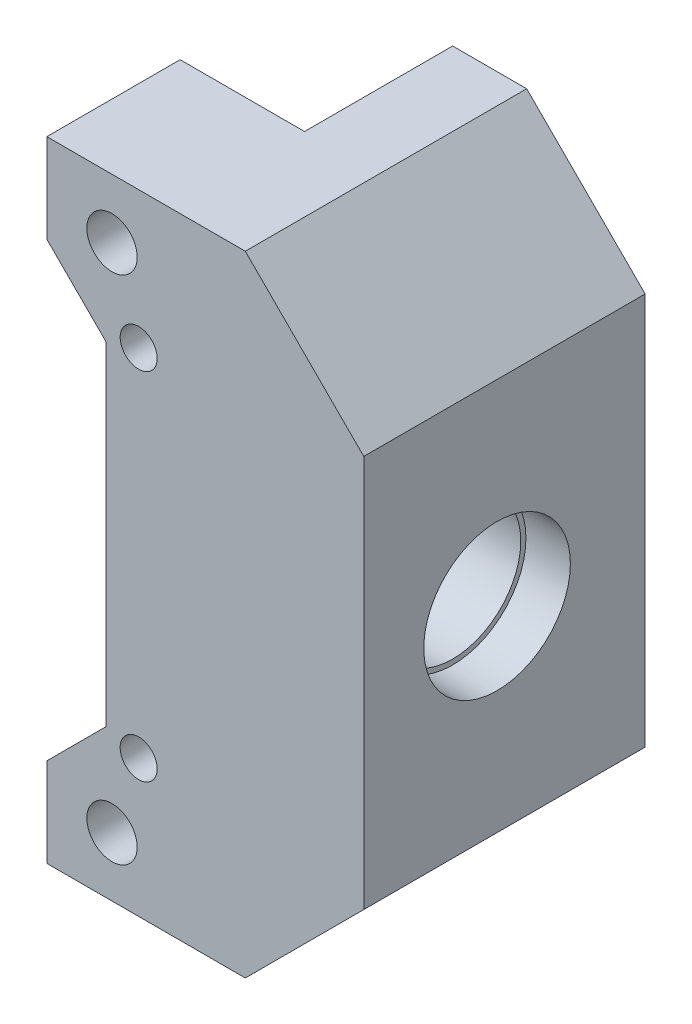
SolidWorks part; units mm, degrees
ref_plane "Plan de face" through (0, 0, 0) normal (0, 0, 1) x (1, 0, 0)
ref_plane "Plan de dessus" through (0, 0, 0) normal (0, 1, 0) x (1, 0, 0)
ref_plane "Plan de droite" through (0, 0, 0) normal (1, 0, 0) x (0, 0, -1)
sketch "Esquisse1" plane through (0, 0, 0) normal (0, 0, 1) x (1, 0, 0)
  line L0 (38.6155, 27.325) -> (38.6155, 15.175)
  line L1 (34.2155, 15.175) -> (34.2155, 27.325)
  line L6 (34.2155, 15.175) -> (34.2155, 10)
  line L7 (34.2155, 10) -> (30.2155, 6)
  line L8 (30.2155, 6) -> (30.2155, 0)
  line L9 (30.2155, 0) -> (38.6155, 0)
  line L10 (38.6155, 0) -> (38.6155, 15.175)
  line L11 (38.6155, 15.175) -> (34.2155, 15.175)
  line L12 (34.2155, 15.175) -> (34.2155, 10)
  line L13 (34.2155, 10) -> (30.2155, 6)
  line L14 (30.2155, 6) -> (30.2155, 0)
  line L15 (30.2155, 0) -> (38.6155, 0)
  line L16 (38.6155, 0) -> (38.6155, 15.175)
  line L18 (30.2155, 42.5) -> (30.2155, 36.5)
  line L19 (30.2155, 36.5) -> (34.2155, 32.5)
  line L20 (34.2155, 32.5) -> (34.2155, 27.325)
  line L21 (34.2155, 27.325) -> (38.6155, 27.325)
  line L22 (38.6155, 27.325) -> (38.6155, 42.5)
  line L23 (38.6155, 42.5) -> (30.2155, 42.5)
  line L24 (30.2155, 42.5) -> (30.2155, 36.5)
  line L25 (30.2155, 36.5) -> (34.2155, 32.5)
  line L26 (34.2155, 32.5) -> (34.2155, 27.325)
  line L28 (38.6155, 27.325) -> (38.6155, 42.5)
  line L29 (38.6155, 42.5) -> (30.2155, 42.5)
  circle A0 centre (34.6155, 4) radius 1.7 construction
  circle A1 centre (34.6155, 4) radius 1.7
  circle A2 centre (34.6155, 38.5) radius 1.7 construction
  circle A3 centre (34.6155, 38.5) radius 1.7
  dimension "D1" = 0
  dimension "D2" = 0
extrude "Boss.-Extru.1" add sketch "Esquisse1" along normal blind 9
sketch "Esquisse2" plane through (0, 0, 9) normal (0, 0, 1) x (1, 0, 0)
  line L0 (38.6155, 0) -> (51.6155, 0)
  line L1 (51.6155, 0) -> (51.6155, 42.5)
  line L2 (51.6155, 42.5) -> (38.6155, 42.5)
  line L3 (38.6155, 42.5) -> (38.6155, 0)
  line L4 (43.6155, 17.25) -> (43.6155, 25.25) construction
  dimension "D1" = 8
extrude "Boss.-Extru.2" add sketch "Esquisse2" against normal up to surface (19 mm away)
sketch "Esquisse4" plane through (34.2155, 0, 0) normal (-1, 0, 0) x (0, 0, 1)
  line L0 (0, 32.5) -> (0, 10) construction
  circle A0 centre (0, 21.25) radius 6.025
  dimension "D1" = 12.05
extrude "Enlèv. mat.-Extru.1" cut sketch "Esquisse4" against normal up to surface (4.4 mm away) up to face at (38.6155, 15.9375, -7.5)
sketch "Esquisse5" plane through (38.6155, 0, 0) normal (-1, 0, 0) x (0, 0, 1)
  line L0 (0, 29.275) -> (-10, 29.275)
  line L1 (-10, 0) -> (-10, 42.5) construction
  line L2 (0, 13.225) -> (-10, 13.225)
  line L3 (-10, 13.225) -> (-10, 29.275)
  arc A0 (0, 13.225) -> (0, 29.275) centre (0, 21.25) ccw
  dimension "D1" = 16.05
extrude "Enlèv. mat.-Extru.2" cut sketch "Esquisse5" against normal blind 5
sketch "Esquisse6" plane through (43.6155, 0, 0) normal (-1, 0, 0) x (0, 0, 1)
  circle A0 centre (0, 21.25) radius 4.6
  dimension "D1" = 9.2
extrude "Enlèv. mat.-Extru.3" cut sketch "Esquisse6" against normal through all
chamfer "Chanfrein1" distance 8 angle 45 2 edges at (51.6155, 42.5, -0.5) (51.6155, 0, -0.5)
hole_wizard "Trou pour taraudage pour trou taraudé M31" positions "Esquisse8" profile "Esquisse7" hole size "M3" standard "Din" end condition through all
sketch "Esquisse8" plane through (0, 0, 9) normal (0, 0, 1) x (1, 0, 0)
  line L0 (36.4155, 9.25) -> (36.4155, 33.25) construction
  line L1 (36.4155, 21.25) -> (34.2155, 21.25) construction
  line L2 (34.2155, 32.5) -> (34.2155, 10) construction
  point P0 (36.4155, 33.25)
  point P2 (36.4155, 9.25)
  dimension "D1" = 24
  dimension "D2" = 2.2
sketch "Esquisse7" plane through (36.4155, 33.25, 9) normal (1, 0, 0) x (0, -1, 0)
  line L0 (0, 0) -> (0, 19)
  line L1 (0, 19) -> (1.25, 19)
  line L2 (1.25, 19) -> (1.25, 0)
  line L5 (1.25, 0) -> (0, 0)
  line L11 (0, -6.35) -> (0, 107.95) construction
  dimension "Diamètre du perçage jusqu'au prochain" = 2.5
  dimension "Profondeur du perçage jusqu'au prochain" = 19
sketch "Esquisse9" plane through (51.6155, 0, 0) normal (1, 0, 0) x (0, 0, -1)
  circle A0 centre (0, 21.25) radius 4.95
  dimension "D1" = 9.9
extrude "Enlèv. mat.-Extru.4" cut sketch "Esquisse9" against normal blind 3
